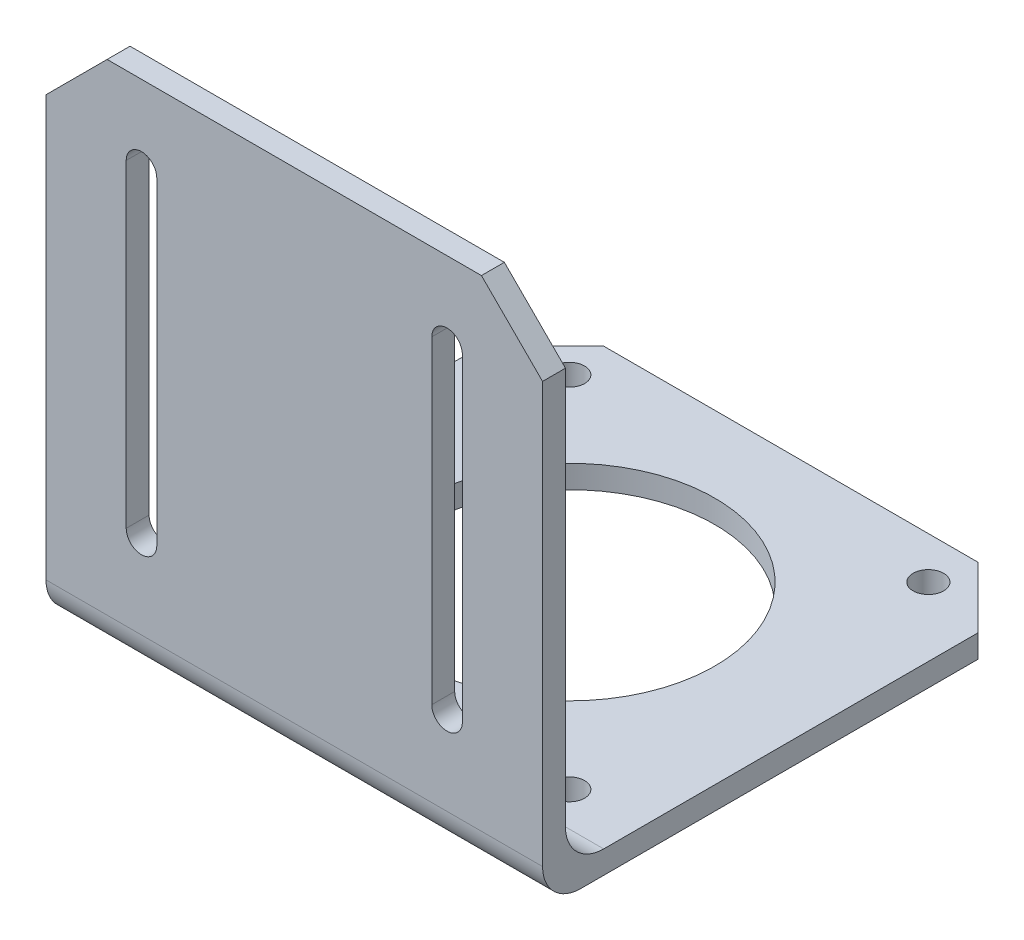
SolidWorks part; units mm, degrees
ref_plane "前基準面" through (0, 0, 0) normal (0, 0, 1) x (1, 0, 0)
ref_plane "上基準面" through (0, 0, 0) normal (0, 1, 0) x (1, 0, 0)
ref_plane "右基準面" through (0, 0, 0) normal (1, 0, 0) x (0, 0, -1)
sketch "草圖2" plane through (0, 0, 0) normal (0, 1, 0) x (1, 0, 0)
  line L0 (0, 0) -> (-32.5, -32.5) construction
  line L1 (-32.5, 32.5) -> (32.5, 32.5)
  line L2 (-32.5, 32.5) -> (-32.5, -32.5)
  line L3 (-32.5, -32.5) -> (32.5, -32.5)
  line L4 (32.5, 32.5) -> (32.5, -32.5)
  line L5 (-23.5, 27) -> (23.5, 27) construction
  line L6 (-23.5, 27) -> (-23.5, -20) construction
  line L7 (-23.5, -20) -> (23.5, -20) construction
  line L8 (23.5, 27) -> (23.5, -20) construction
  line L9 (-23.5, 27) -> (23.5, -20) construction
  line L10 (-23.5, -20) -> (23.5, 27) construction
  line L11 (0, 0) -> (32.5, -32.5) construction
  circle A0 centre (0, 3.5) radius 19.05
  circle A1 centre (-23.5, 27) radius 2
  circle A2 centre (-23.5, -20) radius 2
  circle A3 centre (23.5, -20) radius 2
  circle A4 centre (23.5, 27) radius 2
  point P0 (0, 0)
  point P6 (0, 3.5)
  dimension "D6" = 38.1
  dimension "D7" = 4
  dimension "D1" = 65
  dimension "D2" = 65
  dimension "D3" = 29
  dimension "D4" = 47
  dimension "D5" = 47
extrude "填料-伸長2" add sketch "草圖2" along normal blind 3
chamfer "導角2" distance 8 angle 45 2 edges at (32.5, 1.5, -32.5) (-32.5, 1.5, -32.5)
sketch "草圖3" plane through (0, 3, 0) normal (0, 1, 0) x (1, 0, 0)
  line L0 (32.5, -32.5) -> (32.5, 24.5) construction
  line L1 (-32.5, -32.5) -> (32.5, -32.5)
  line L2 (-32.5, -32.5) -> (-32.5, -29.5)
  line L3 (-32.5, -29.5) -> (32.5, -29.5)
  line L4 (32.5, -32.5) -> (32.5, -29.5)
  dimension "D1" = 3
extrude "填料-伸長3" add sketch "草圖3" along normal blind 65
fillet "圓角1" radius 5 2 edges at (0, 3, 29.5) (0, 0, 32.5)
chamfer "導角3" distance 8 angle 45 2 edges at (32.5, 68, 31) (-32.5, 68, 31)
sketch "草圖4" plane through (0, 0, 29.5) normal (0, 0, -1) x (-1, 0, 0)
  line L0 (0, 0) -> (0, 68) construction
  line L1 (-20, 16.1) -> (20, 16.1) construction
  line L2 (-20, 16.1) -> (-20, 57.8) construction
  line L3 (-20, 57.8) -> (20, 57.8) construction
  line L4 (20, 16.1) -> (20, 57.8) construction
  line L5 (-20, 16.1) -> (20, 57.8) construction
  line L6 (-20, 57.8) -> (20, 16.1) construction
  line L7 (-24.5, 68) -> (24.5, 68) construction
  line L8 (-20, 57.8) -> (-20, 16.1) construction
  line L9 (-18, 57.8) -> (-18, 16.1)
  line L10 (-22, 57.8) -> (-22, 16.1)
  line L11 (20, 57.8) -> (20, 16.1) construction
  line L12 (18, 57.8) -> (18, 16.1)
  line L13 (22, 57.8) -> (22, 16.1)
  arc A0 (-18, 57.8) -> (-22, 57.8) centre (-20, 57.8) ccw
  arc A1 (-22, 16.1) -> (-18, 16.1) centre (-20, 16.1) ccw
  arc A2 (18, 57.8) -> (22, 57.8) centre (20, 57.8) cw
  arc A3 (22, 16.1) -> (18, 16.1) centre (20, 16.1) cw
  point P0 (0, 36.95)
  point P10 (-20, 36.95)
  point P15 (20, 36.95)
  dimension "D4" = 2
  dimension "D1" = 40
  dimension "D2" = 41.7
  dimension "D3" = 10.2
extrude "除料-伸長1" cut sketch "草圖4" against normal blind 65
